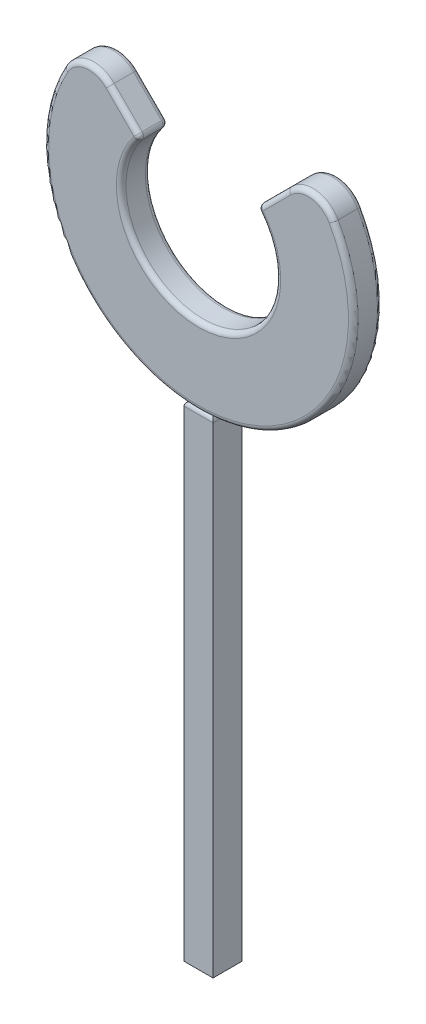
SolidWorks part; units mm, degrees
ref_plane "Front Plane" through (0, 0, 0) normal (0, 0, 1) x (1, 0, 0)
ref_plane "Top Plane" through (0, 0, 0) normal (0, 1, 0) x (1, 0, 0)
ref_plane "Right Plane" through (0, 0, 0) normal (1, 0, 0) x (0, 0, -1)
sketch "Sketch1" plane through (0, 0, 0) normal (0, 0, 1) x (1, 0, 0)
  circle A0 centre (0, 0) radius 8
  circle A1 centre (0, 0) radius 16
  point P4 (0, 0)
  dimension "D1" = 16
  dimension "D2" = 8
extrude "Boss-Extrude1" add sketch "Sketch1" along normal blind 3
sketch "Sketch2" plane through (0, 0, 3) normal (0, 0, 1) x (1, 0, 0)
  line L1 (-6, 5.2915) -> (6, 5.2915)
  line L2 (6, 5.2915) -> (18, 17.2915)
  line L3 (18, 17.2915) -> (-18, 17.2915)
  line L4 (-18, 17.2915) -> (-6, 5.2915)
  circle A3 centre (0, 0) radius 8 construction
  point P4 (16.5868, 17.2915)
  dimension "D1" = 12
  dimension "D2" = 90
  dimension "D3" = 12
extrude "Cut-Extrude1" cut sketch "Sketch2" against normal blind 3
fillet "Fillet1" radius 3 2 edges at (-11.6624, 10.9539, 1.5) (11.6624, 10.9539, 1.5)
fillet "Fillet2" radius 0.5 14 edges at (0, -8, 3) (7.6035, 6.895, 3) (11.7361, 9.3494, 3) (0, -16, 3) (-11.7361, 9.3494, 3) (-7.6035, 6.895, 3) (11.7361, 9.3494, 0) (7.6035, 6.895, 0) (0, -8, 0) (-7.6035, 6.895, 0) (-11.7361, 9.3494, 0) (0, -16, 0) (6, 5.2915, 1.5) (-6, 5.2915, 1.5)
ref_plane "Plane1" through (0, -16, 0) normal (0, -1, 0) x (-1, 0, 0)
sketch "Sketch3" plane through (0, -16, 0) normal (0, -1, 0) x (-1, 0, 0)
  line L0 (-15.5, -3) -> (15.5, -3) construction
  line L1 (1.5, -3) -> (-1.5, -3)
  line L2 (1.5, -3) -> (1.5, 0)
  line L3 (1.5, 0) -> (-1.5, 0)
  line L4 (-1.5, -3) -> (-1.5, 0)
  line L5 (15.5, 0) -> (-15.5, 0) construction
  point P8 (0, 0)
  dimension "D1" = 3
extrude "Boss-Extrude2" add sketch "Sketch3" along normal blind 50 and the other way blind 0.2 separate body
fillet "Fillet3" radius 0.5 4 edges at (0, -15.8, 0) (1.5, -15.8, 1.5) (0, -15.8, 3) (-1.5, -15.8, 1.5)
